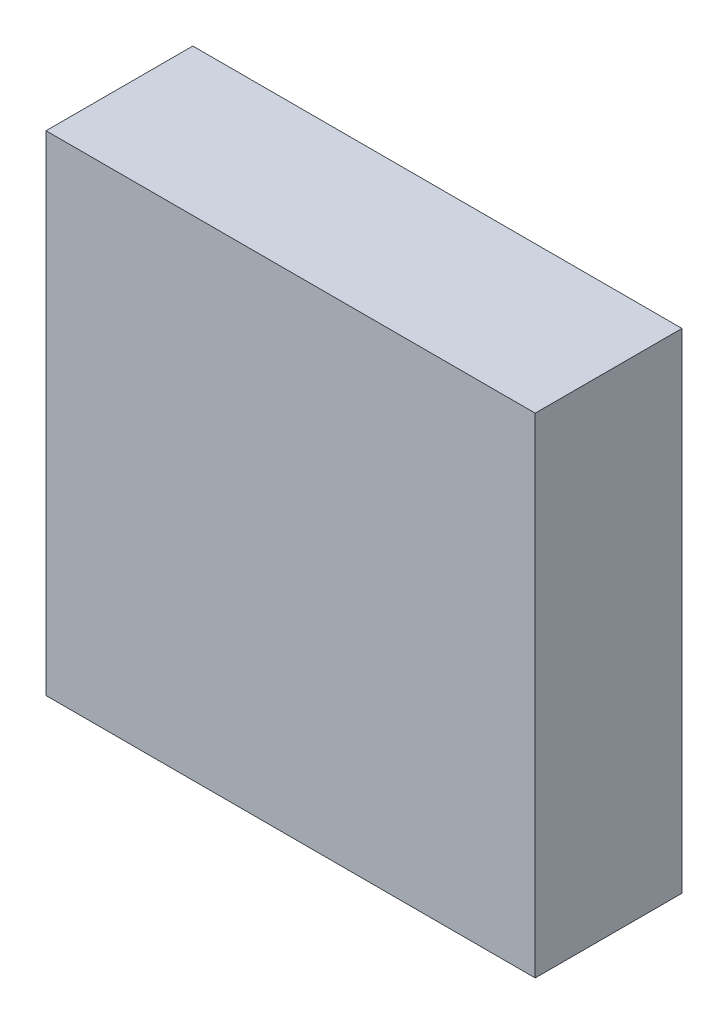
SolidWorks part; units mm, degrees
ref_plane "Front Plane" through (0, 0, 0) normal (0, 0, 1) x (1, 0, 0)
ref_plane "Top Plane" through (0, 0, 0) normal (0, 1, 0) x (1, 0, 0)
ref_plane "Right Plane" through (0, 0, 0) normal (1, 0, 0) x (0, 0, -1)
sketch "Sketch1" plane through (0, 0, 0) normal (0, 0, 1) x (1, 0, 0)
  line L1 (-50, 50) -> (50, 50)
  line L2 (-50, 50) -> (-50, -50)
  line L3 (-50, -50) -> (50, -50)
  line L4 (50, 50) -> (50, -50)
  line L5 (-50, 50) -> (50, -50) construction
  line L6 (-50, -50) -> (50, 50) construction
  point P0 (0, 0)
  dimension "D1" = 50
  dimension "D2" = 100
  dimension "D3" = 50
  dimension "D4" = 100
extrude "Boss-Extrude1" add sketch "Sketch1" along normal blind 30
